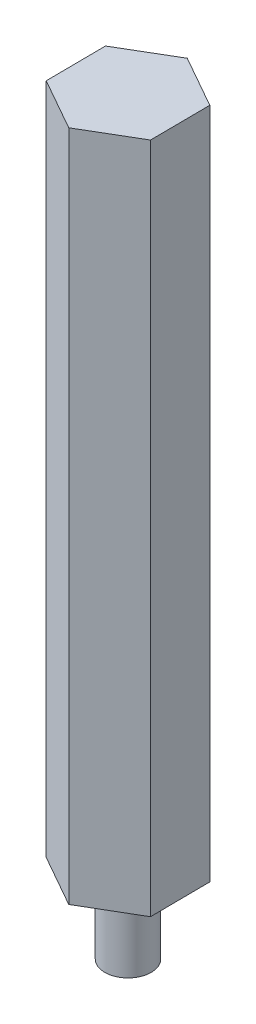
SolidWorks part; units mm, degrees
ref_plane "Front Plane" through (0, 0, 0) normal (0, 0, 1) x (1, 0, 0)
ref_plane "Top Plane" through (0, 0, 0) normal (0, 1, 0) x (1, 0, 0)
ref_plane "Right Plane" through (0, 0, 0) normal (1, 0, 0) x (0, 0, -1)
sketch "Sketch1" plane through (0, 0, 0) normal (0, 1, 0) x (1, 0, 0)
  line L1 (3.1898, -1.8072) -> (3.16, 1.8589)
  line L2 (3.16, 1.8589) -> (-0.0299, 3.6661)
  line L3 (-0.0299, 3.6661) -> (-3.1898, 1.8072)
  line L4 (-3.1898, 1.8072) -> (-3.16, -1.8589)
  line L5 (-3.16, -1.8589) -> (0.0299, -3.6661)
  line L6 (0.0299, -3.6661) -> (3.1898, -1.8072)
  circle A0 centre (0, 0) radius 3.175 construction
  dimension "D1" = 6.35
extrude "Boss-Extrude1" add sketch "Sketch1" along normal blind 41.28
sketch "Sketch3" plane through (0, 0, 0) normal (0, -1, 0) x (-1, 0, 0)
  circle A0 centre (0, 0) radius 1.4224
  dimension "D1" = 2.8448
extrude "Boss-Extrude2" add sketch "Sketch3" along normal blind 4.75
